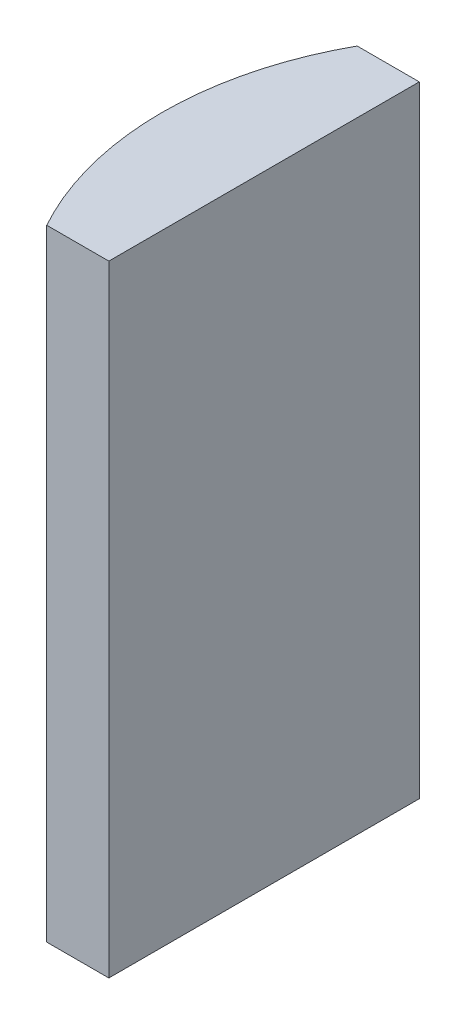
SolidWorks part; units mm, degrees
ref_plane "前视基准面" through (0, 0, 0) normal (0, 0, 1) x (1, 0, 0)
ref_plane "上视基准面" through (0, 0, 0) normal (0, 1, 0) x (1, 0, 0)
ref_plane "右视基准面" through (0, 0, 0) normal (1, 0, 0) x (0, 0, -1)
sketch "草图1" plane through (0, 0, 0) normal (0, 1, 0) x (1, 0, 0)
  line L0 (10.7432, 0) -> (-19.1624, 0) construction
  line L1 (-4.6955, 5) -> (-2.6948, 5)
  line L2 (-4.6955, -5) -> (-2.6948, -5)
  line L3 (-2.6948, 5) -> (-2.6948, -5)
  arc A0 (-4.6955, 5) -> (-4.6955, -5) centre (4.3552, 0) ccw
  point P19 (-5.9848, 0)
  point P20 (-2.6948, 0)
  dimension "D2" = 5
  dimension "D3" = 10.34
  dimension "D4" = 3.29
  dimension "D1" = 5
extrude "凸台-拉伸1" add sketch "草图1" along normal blind 20
